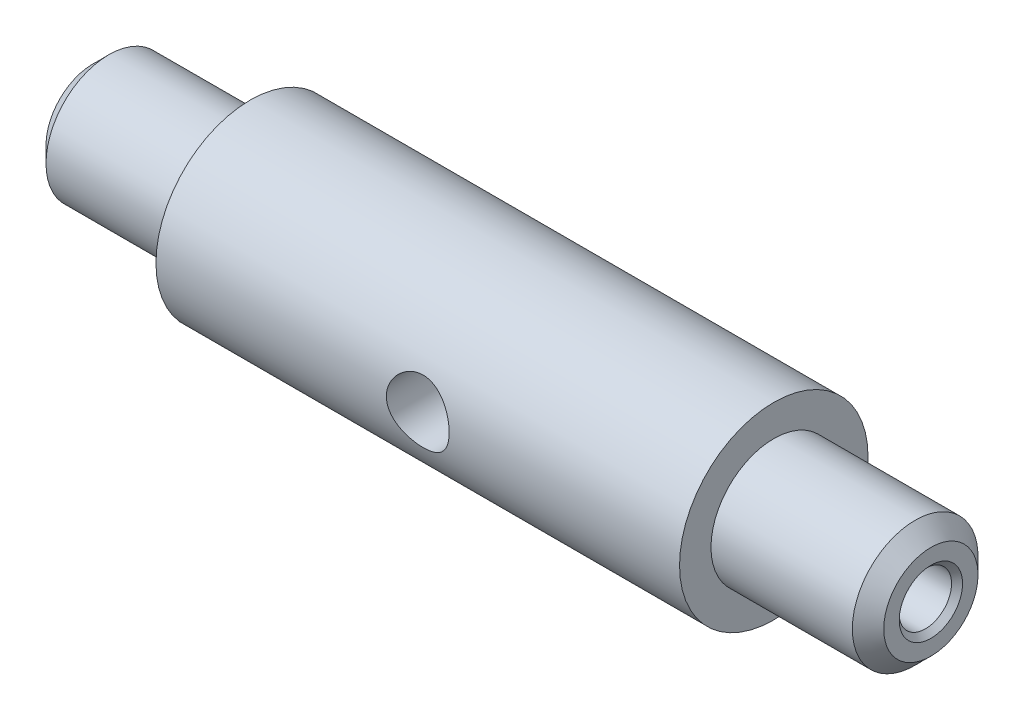
SolidWorks part; units mm, degrees
ref_plane "Front Plane" through (0, 0, 0) normal (0, 0, 1) x (1, 0, 0)
ref_plane "Top Plane" through (0, 0, 0) normal (0, 1, 0) x (1, 0, 0)
ref_plane "Right Plane" through (0, 0, 0) normal (1, 0, 0) x (0, 0, -1)
sketch "Sketch1" plane through (0, 0, 0) normal (0, 1, 0) x (1, 0, 0)
  line L1 (0, 6) -> (15, 6)
  line L2 (15, 6) -> (15, 9)
  line L3 (15, 9) -> (65, 9)
  line L4 (65, 9) -> (65, 6)
  line L5 (65, 6) -> (80, 6)
  line L7 (0, 0) -> (80, 0) construction
  line L17 (0, 6) -> (0, 0)
  line L18 (0, 0) -> (80, 0)
  line L19 (80, 6) -> (80, 0)
revolve "Revolve4" add sketch "Sketch1" angle 360 about L18
hole_wizard "M6x1.0 Tapped Hole1" positions "Sketch2" profile "Sketch4" tap size "M6x1.0" standard "ANSI Metric"
sketch "Sketch2" plane through (80, 0, 0) normal (1, 0, 0) x (0, 0, -1)
  point P0 (0, 0)
sketch "Sketch4" plane through (80, 0, 0) normal (0, 1, 0) x (0, 0, -1)
  line L0 (0, 0) -> (0, 46.5022)
  line L1 (0, 46.5022) -> (2.5, 45)
  line L2 (2.5, 45) -> (2.5, 0.525)
  line L3 (2.5, 0.525) -> (3.025, 0)
  line L5 (3.025, 0) -> (0, 0)
  line L6 (-2.5, 0.525) -> (-3.025, 0) construction
  line L10 (0, 46.5022) -> (-2.5, 45) construction
  line L11 (0, -6.35) -> (0, 107.95) construction
  dimension "Tap Drill Dia." = 5
  dimension "Tap Drill Depth" = 45
  dimension "Near C'Sink Dia." = 6.05
  dimension "Near C'Sink Angle" = 90
  dimension "Drill Angle" = 118
cosmetic thread "Hole Thread1" parameters "D1"=12, "D2"=6
sketch "Sketch5" plane through (0, 0, 0) normal (0, 0, 1) x (1, 0, 0)
  line L0 (9.9, 0) -> (-9.9, 0) construction
  line L1 (15, 9) -> (15, -9) construction
  circle A0 centre (40, 0) radius 3
  dimension "D1" = 25
extrude "Cut-Extrude1" cut sketch "Sketch5" against normal through all both and the other way through all
chamfer "Chamfer1" distance 1.5 angle 45 2 edges at (0, 0, 6) (80, 0, 6)
